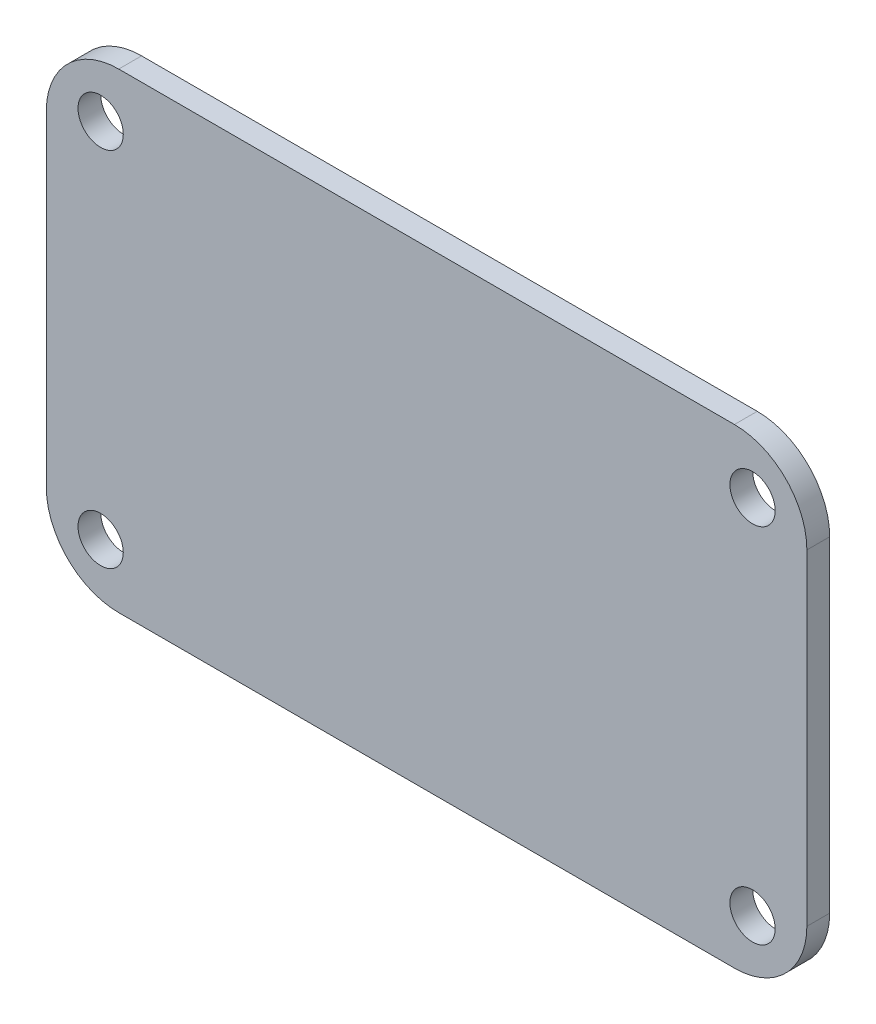
SolidWorks part; units mm, degrees
ref_plane "Front Plane" through (0, 0, 0) normal (0, 0, 1) x (1, 0, 0)
ref_plane "Top Plane" through (0, 0, 0) normal (0, 1, 0) x (1, 0, 0)
ref_plane "Right Plane" through (0, 0, 0) normal (1, 0, 0) x (0, 0, -1)
sketch "Sketch1" plane through (0, 0, 0) normal (0, 0, 1) x (1, 0, 0)
  line L1 (-21.59, 16.51) -> (21.59, 16.51)
  line L2 (-26.67, 11.43) -> (-26.67, -11.43)
  line L3 (-21.59, -16.51) -> (21.59, -16.51)
  line L4 (26.67, 11.43) -> (26.67, -11.43)
  line L5 (-26.67, 16.51) -> (26.67, -16.51) construction
  line L6 (-26.67, -16.51) -> (26.67, 16.51) construction
  arc A0 (-26.67, -11.43) -> (-21.59, -16.51) centre (-21.59, -11.43) ccw
  arc A1 (21.59, -16.51) -> (26.67, -11.43) centre (21.59, -11.43) ccw
  arc A2 (21.59, 16.51) -> (26.67, 11.43) centre (21.59, 11.43) cw
  arc A3 (-21.59, 16.51) -> (-26.67, 11.43) centre (-21.59, 11.43) ccw
  point P0 (0, 0)
  dimension "D3" = 5.08
  dimension "D1" = 53.34
  dimension "D2" = 33.02
extrude "Boss-Extrude1" add sketch "Sketch1" against normal blind 1.6002
sketch "Sketch2" plane through (0, 0, 0) normal (0, 0, 1) x (1, 0, 0)
  circle A0 centre (-22.86, 12.7) radius 1.5875
  circle A1 centre (-22.86, -12.7) radius 1.5875
  circle A2 centre (22.86, 12.7) radius 1.5875
  circle A3 centre (22.86, -12.7) radius 1.5875
  dimension "D4" = 3.175
  dimension "D5" = 3.175
  dimension "D6" = 3.175
  dimension "D7" = 3.175
  dimension "D9" = 22.86
  dimension "D1" = 25.4
  dimension "D2" = 25.4
  dimension "D3" = 45.72
  dimension "D8" = 12.7
extrude "Cut-Extrude1" cut sketch "Sketch2" against normal blind 11.7602
